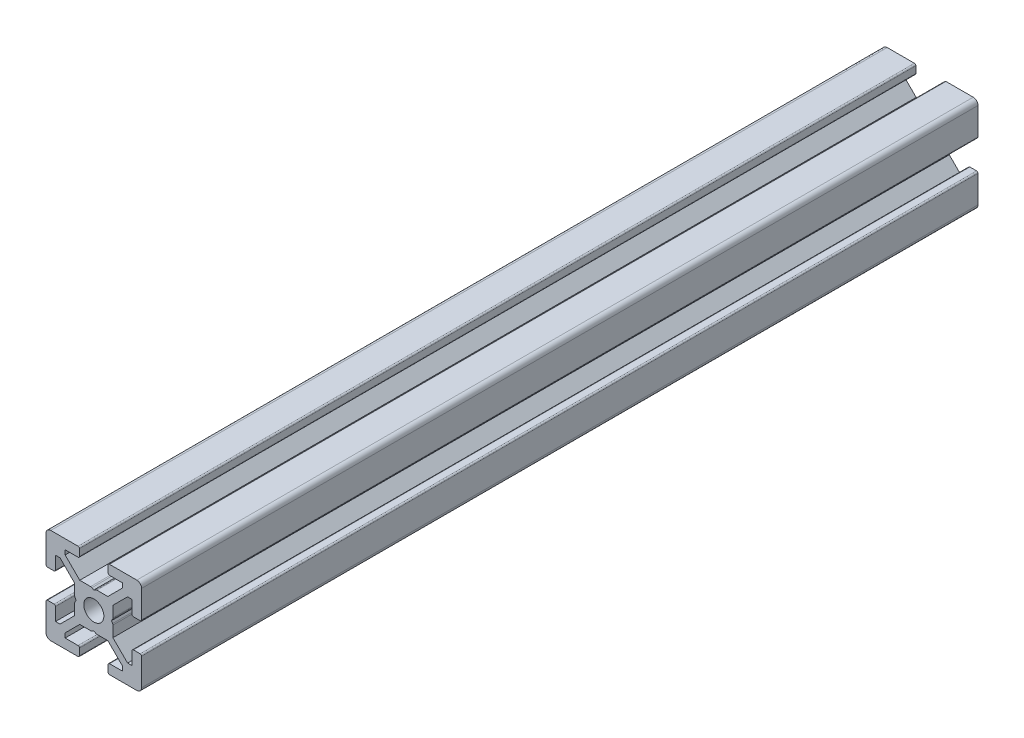
SolidWorks part; units mm, degrees
ref_plane "Front Plane" through (0, 0, 0) normal (0, 0, 1) x (1, 0, 0)
ref_plane "Top Plane" through (0, 0, 0) normal (0, 1, 0) x (1, 0, 0)
ref_plane "Right Plane" through (0, 0, 0) normal (1, 0, 0) x (0, 0, -1)
sketch "Model" plane through (0, 0, 0) normal (0, 0, 1) x (1, 0, 0)
  line L0 (-3, 8.3) -> (-3, 9.7)
  line L1 (-6, 7.0607) -> (-6, 8)
  line L2 (-3.3, 8) -> (-6, 8)
  line L3 (-3.3, 10) -> (-9, 10)
  line L4 (-0.4036, 3.933) -> (0, 3.7)
  line L5 (-0.6536, 4) -> (-2.9393, 4)
  line L6 (-2.9393, 4) -> (-6, 7.0607)
  line L7 (-4, 2.9393) -> (-4, 0.6536)
  line L8 (-8, 6) -> (-8, 3.3)
  line L9 (-7.0607, 6) -> (-8, 6)
  line L10 (-8.3, 3) -> (-9.7, 3)
  line L11 (-8.3, -3) -> (-9.7, -3)
  line L12 (-7.0607, -6) -> (-8, -6)
  line L13 (-8, -3.3) -> (-8, -6)
  line L14 (-10, -3.3) -> (-10, -9)
  line L15 (-3.933, 0.4036) -> (-3.7, 0)
  line L16 (-3.933, -0.4036) -> (-3.7, 0)
  line L17 (-4, 2.9393) -> (-7.0607, 6)
  line L18 (-4, -0.6536) -> (-4, -2.9393)
  line L19 (-10, 3.3) -> (-10, 9)
  line L20 (-4, -2.9393) -> (-7.0607, -6)
  line L23 (-2.9393, -4) -> (-0.6536, -4)
  line L24 (8.3, 3) -> (9.7, 3)
  line L25 (-6, -8) -> (-3.3, -8)
  line L26 (7.0607, 6) -> (8, 6)
  line L27 (8, 3.3) -> (8, 6)
  line L28 (-6, -7.0607) -> (-6, -8)
  line L29 (10, 3.3) -> (10, 9)
  line L30 (-3, -8.3) -> (-3, -9.7)
  line L31 (3.933, 0.4036) -> (3.7, 0)
  line L32 (-0.4036, -3.933) -> (0, -3.7)
  line L33 (4, 0.6536) -> (4, 2.9393)
  line L34 (-2.9393, -4) -> (-6, -7.0607)
  line L35 (4, 2.9393) -> (7.0607, 6)
  line L36 (2.9393, 4) -> (0.6536, 4)
  line L37 (-3.3, -10) -> (-9, -10)
  line L38 (6, 8) -> (3.3, 8)
  line L39 (6, 7.0607) -> (6, 8)
  line L40 (3, 8.3) -> (3, 9.7)
  line L41 (0.4036, 3.933) -> (0, 3.7)
  line L44 (2.9393, 4) -> (6, 7.0607)
  line L45 (3.3, 10) -> (9, 10)
  line L48 (3, -8.3) -> (3, -9.7)
  line L49 (6, -7.0607) -> (6, -8)
  line L50 (3.3, -8) -> (6, -8)
  line L51 (3.3, -10) -> (9, -10)
  line L52 (0.4036, -3.933) -> (0, -3.7)
  line L53 (0.6536, -4) -> (2.9393, -4)
  line L54 (2.9393, -4) -> (6, -7.0607)
  line L55 (4, -2.9393) -> (4, -0.6536)
  line L56 (8, -6) -> (8, -3.3)
  line L57 (7.0607, -6) -> (8, -6)
  line L58 (8.3, -3) -> (9.7, -3)
  line L59 (3.933, -0.4036) -> (3.7, 0)
  line L60 (4, -2.9393) -> (7.0607, -6)
  line L61 (10, -3.3) -> (10, -9)
  arc A0 (-3.933, -0.4036) -> (-4, -0.6536) centre (-3.5, -0.6536) ccw
  arc A1 (-0.4036, 3.933) -> (-0.6536, 4) centre (-0.6536, 3.5) ccw
  arc A2 (-3.3, 8) -> (-3, 8.3) centre (-3.3, 8.3) ccw
  arc A3 (-3, 9.7) -> (-3.3, 10) centre (-3.3, 9.7) ccw
  arc A4 (-8, -3.3) -> (-8.3, -3) centre (-8.3, -3.3) ccw
  arc A5 (-9.7, -3) -> (-10, -3.3) centre (-9.7, -3.3) ccw
  arc A6 (-3.3, -10) -> (-3, -9.7) centre (-3.3, -9.7) ccw
  arc A7 (-3, -8.3) -> (-3.3, -8) centre (-3.3, -8.3) ccw
  arc A8 (-10, 3.3) -> (-9.7, 3) centre (-9.7, 3.3) ccw
  arc A9 (-8.3, 3) -> (-8, 3.3) centre (-8.3, 3.3) ccw
  arc A10 (-0.6536, -4) -> (-0.4036, -3.933) centre (-0.6536, -3.5) ccw
  arc A11 (-4, 0.6536) -> (-3.933, 0.4036) centre (-3.5, 0.6536) ccw
  arc A12 (-2.1, 0) -> (0, -2.1) centre (0, 0) ccw
  arc A13 (0, 2.1) -> (-2.1, 0) centre (0, 0) ccw
  arc A14 (-9, 10) -> (-10, 9) centre (-9, 9) ccw
  arc A15 (3.933, 0.4036) -> (4, 0.6536) centre (3.5, 0.6536) ccw
  arc A16 (-10, -9) -> (-9, -10) centre (-9, -9) ccw
  arc A17 (8, 3.3) -> (8.3, 3) centre (8.3, 3.3) ccw
  arc A18 (9.7, 3) -> (10, 3.3) centre (9.7, 3.3) ccw
  arc A19 (3.3, 10) -> (3, 9.7) centre (3.3, 9.7) ccw
  arc A20 (3, 8.3) -> (3.3, 8) centre (3.3, 8.3) ccw
  arc A21 (0.6536, 4) -> (0.4036, 3.933) centre (0.6536, 3.5) ccw
  arc A22 (2.1, 0) -> (0, 2.1) centre (0, 0) ccw
  arc A23 (10, 9) -> (9, 10) centre (9, 9) ccw
  arc A24 (0.4036, -3.933) -> (0.6536, -4) centre (0.6536, -3.5) ccw
  arc A25 (3.3, -8) -> (3, -8.3) centre (3.3, -8.3) ccw
  arc A26 (3, -9.7) -> (3.3, -10) centre (3.3, -9.7) ccw
  arc A27 (10, -3.3) -> (9.7, -3) centre (9.7, -3.3) ccw
  arc A28 (8.3, -3) -> (8, -3.3) centre (8.3, -3.3) ccw
  arc A29 (4, -0.6536) -> (3.933, -0.4036) centre (3.5, -0.6536) ccw
  arc A30 (0, -2.1) -> (2.1, 0) centre (0, 0) ccw
  arc A31 (9, -10) -> (10, -9) centre (9, -9) ccw
  point P128 (0, 0)
  dimension "D1" = 4
extrude "Boss-Extrude1" add sketch "Model" along normal blind 175
